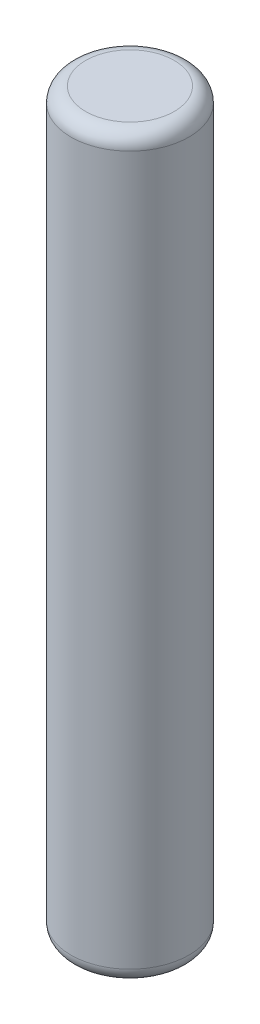
SolidWorks part; units mm, degrees
ref_plane "Front Plane" through (0, 0, 0) normal (0, 0, 1) x (1, 0, 0)
ref_plane "Top Plane" through (0, 0, 0) normal (0, 1, 0) x (1, 0, 0)
ref_plane "Right Plane" through (0, 0, 0) normal (1, 0, 0) x (0, 0, -1)
sketch "Sketch1" plane through (0, 0, 0) normal (0, 1, 0) x (1, 0, 0)
  circle A0 centre (0, 0) radius 4
  dimension "D1" = 8
extrude "Boss-Extrude1" add sketch "Sketch1" along normal blind 50
fillet "Fillet1" radius 1 1 edges at (0, 50, 4)
fillet "Fillet2" radius 1 1 edges at (0, 0, 4)
